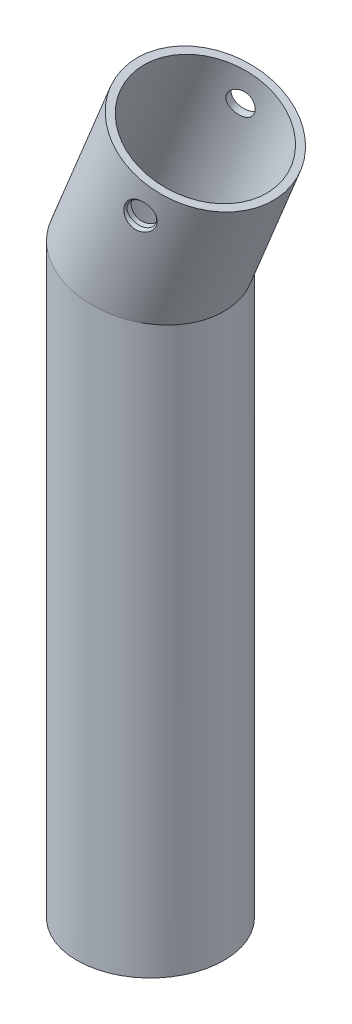
SolidWorks part; units mm, degrees
ref_plane "Спереди" through (0, 0, 0) normal (0, 0, 1) x (1, 0, 0)
ref_plane "Сверху" through (0, 0, 0) normal (0, 1, 0) x (1, 0, 0)
ref_plane "Справа" through (0, 0, 0) normal (1, 0, 0) x (0, 0, -1)
other "Configuration Table"
sketch "Эскиз1" plane through (0, 0, 0) normal (0, 1, 0) x (1, 0, 0)
  circle A0 centre (0, 0) radius 10
  circle A1 centre (0, 0) radius 9
  dimension "20" = 20
  dimension "D2" = 18
sketch "Эскиз2" plane through (0, 0, 0) normal (0, 0, 1) x (1, 0, 0)
  line L0 (0, 0) -> (0, 78.4265)
  line L1 (10, 0) -> (-10, 0) construction
  line L2 (0, 78.4265) -> (7.4714, 96.6909)
sweep "По траектории2" add profiles "Эскиз1" path "Эскиз2"
hole_wizard "Отверстие обработанное метчиком M4x0.71" positions "Трехмерный эскиз1" profile "Эскиз3" tap size "M4x0.7" standard "JIS" end condition through all
sketch3d "Трехмерный эскиз1"
  point P0 (8.2056, 91.6429, 9.6586)
sketch "Эскиз3" plane through (8.2056, 91.6429, 9.6586) normal (0.7033, 0.7033, -0.1032) x (0.6692, -0.7041, -0.2376)
  line L0 (0, 0) -> (0, 24.2194)
  line L1 (0, 24.2194) -> (1.65, 24.2194)
  line L2 (1.65, 24.2194) -> (1.65, 0.375)
  line L3 (1.65, 0.375) -> (2.025, 0)
  line L5 (2.025, 0) -> (0, 0)
  line L6 (-1.65, 0.375) -> (-2.025, 0) construction
  line L11 (0, -6.35) -> (0, 107.95) construction
  dimension "Диаметр проходного сверла" = 3.3
  dimension "Глубина проходного сверла" = 24.2194
  dimension "Диаметр передней зенковки" = 4.05
  dimension "Угол передней зенковки" = 90
cosmetic thread "Отверстие резьбы1" parameters "D2"=4
